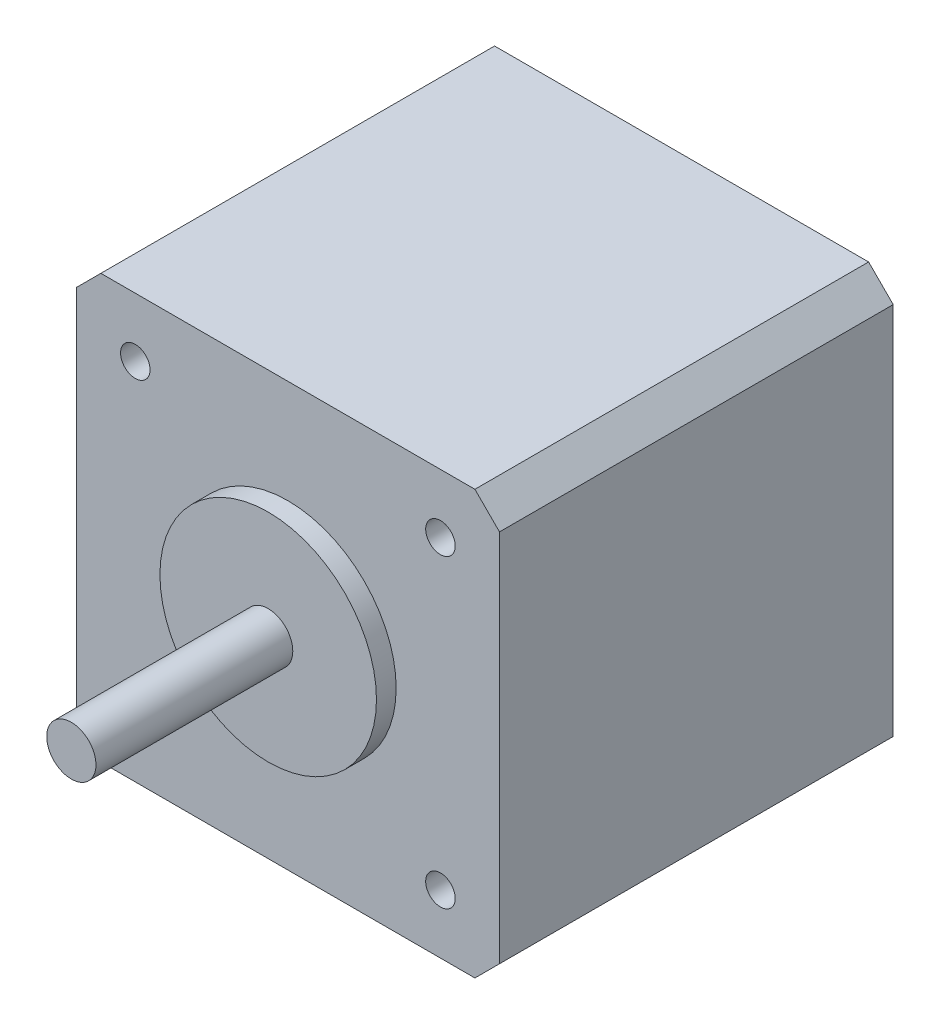
SolidWorks part; units mm, degrees
ref_plane "Front Plane" through (0, 0, 0) normal (0, 0, 1) x (1, 0, 0)
ref_plane "Top Plane" through (0, 0, 0) normal (0, 1, 0) x (1, 0, 0)
ref_plane "Right Plane" through (0, 0, 0) normal (1, 0, 0) x (0, 0, -1)
sketch "Sketch1" plane through (0, 0, 0) normal (0, 0, 1) x (1, 0, 0)
  line L1 (-21.5, -21.5) -> (21.5, -21.5)
  line L2 (-21.5, -21.5) -> (-21.5, 21.5)
  line L3 (-21.5, 21.5) -> (21.5, 21.5)
  line L4 (21.5, -21.5) -> (21.5, 21.5)
  line L5 (-21.5, -21.5) -> (21.5, 21.5) construction
  line L6 (-21.5, 21.5) -> (21.5, -21.5) construction
  point P0 (0, 0)
extrude "Boss-Extrude1" add sketch "Sketch1" along normal blind 40
chamfer "Chamfer1" distance 2.5 angle 45 4 edges at (-21.5, -21.5, 20) (21.5, -21.5, 20) (-21.5, 21.5, 20) (21.5, 21.5, 20)
sketch "Sketch2" plane through (0, 0, 40) normal (0, 0, 1) x (1, 0, 0)
  circle A0 centre (0, 0) radius 11
extrude "Boss-Extrude2" add sketch "Sketch2" along normal blind 2
sketch "Sketch3" plane through (0, 0, 42) normal (0, 0, 1) x (1, 0, 0)
  circle A0 centre (0, 0) radius 2.5
extrude "Boss-Extrude3" add sketch "Sketch3" along normal blind 20
sketch "Sketch4" plane through (0, 0, 40) normal (0, 0, 1) x (1, 0, 0)
  line L2 (19, 21.5) -> (-19, 21.5) construction
  line L3 (-21.5, 19) -> (-21.5, -19) construction
  circle A0 centre (-15.5, 15.5) radius 1.5
  circle A1 centre (15.5, 15.5) radius 1.5
  circle A2 centre (15.5, -15.5) radius 1.5
  circle A3 centre (-15.5, -15.5) radius 1.5
  dimension "D3" = 4
  dimension "D1" = 6
  dimension "D2" = 6
extrude "Cut-Extrude1" cut sketch "Sketch4" against normal blind 10
